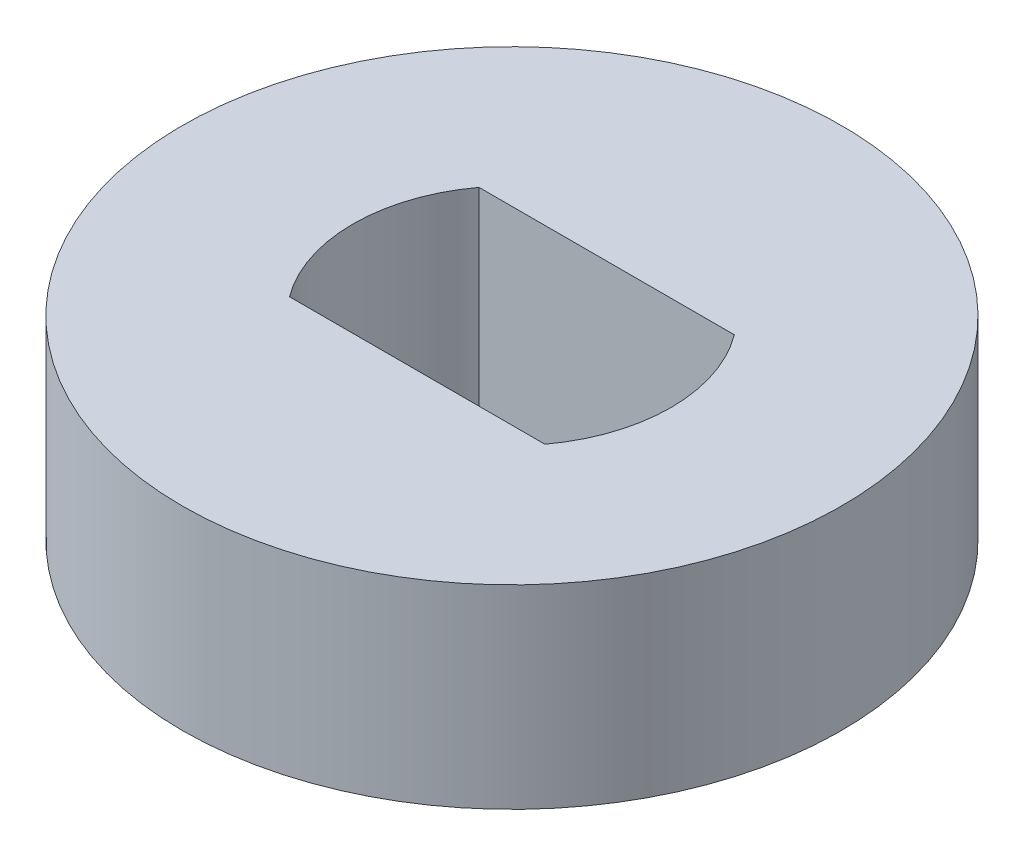
SolidWorks part; units mm, degrees
ref_plane "Front Plane" through (0, 0, 0) normal (0, 0, 1) x (1, 0, 0)
ref_plane "Top Plane" through (0, 0, 0) normal (0, 1, 0) x (1, 0, 0)
ref_plane "Right Plane" through (0, 0, 0) normal (1, 0, 0) x (0, 0, -1)
sketch "Sketch1" plane through (0, 0, 0) normal (0, 1, 0) x (1, 0, 0)
  line L0 (-1.9685, 1.4605) -> (1.9685, 1.4605)
  line L2 (1.9685, -1.4605) -> (-1.9685, -1.4605)
  arc A0 (-1.9685, 1.4605) -> (-1.9685, -1.4605) centre (0, 0) ccw
  circle A1 centre (0, 0) radius 5.08
  arc A2 (1.9685, -1.4605) -> (1.9685, 1.4605) centre (0, 0) ccw
  dimension "D1" = 3.937
  dimension "D3" = 10.16
  dimension "D2" = 2.921
extrude "Boss-Extrude1" add sketch "Sketch1" along normal blind 2.9972
